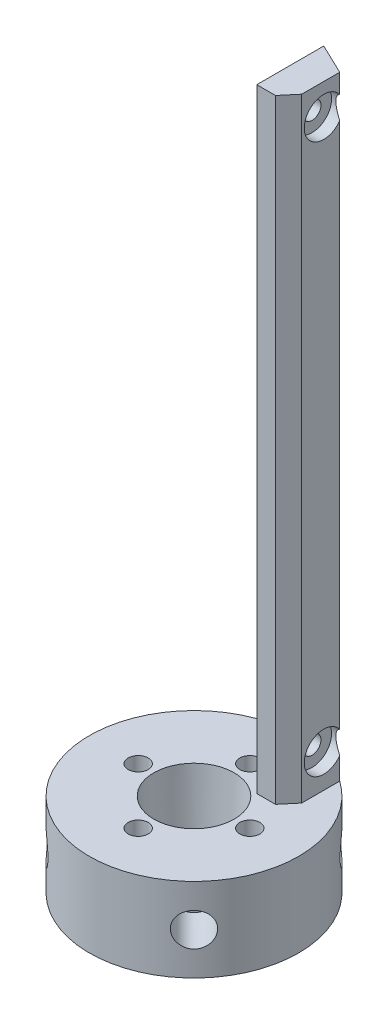
SolidWorks part; units mm, degrees
ref_plane "Ebene vorne" through (0, 0, 0) normal (0, 0, 1) x (1, 0, 0)
ref_plane "Ebene oben" through (0, 0, 0) normal (0, 1, 0) x (1, 0, 0)
ref_plane "Ebene rechts" through (0, 0, 0) normal (1, 0, 0) x (0, 0, -1)
sketch "Skizze1" plane through (0, 0, 0) normal (0, 1, 0) x (1, 0, 0)
  circle A0 centre (0, 0) radius 18.75
  dimension "D1" = 37.5
extrude "Aufsatz-Linear austragen1" add sketch "Skizze1" along normal blind 15
sketch "Skizze2" plane through (0, 15, 0) normal (0, 1, 0) x (1, 0, 0)
  circle A0 centre (0, 10) radius 1.8
  circle A1 centre (10, 0) radius 1.8
  circle A2 centre (0, -10) radius 1.8
  circle A3 centre (-10, 0) radius 1.8
  circle A4 centre (0, 0) radius 1.65
  point P12 (0, 0)
  dimension "D1" = 3.6
  dimension "D5" = 3.3
  dimension "D2" = 0
  dimension "D3" = 10
  dimension "D4" = 4
extrude "Schnitt-Linear austragen1" cut sketch "Skizze2" against normal through all
sketch "Skizze4" plane through (0, 15, 0) normal (0, 1, 0) x (1, 0, 0)
  line L0 (5.25, 17) -> (5.25, 6)
  line L4 (8.6073, 6) -> (10.7509, 8.5546)
  line L5 (5.25, 17) -> (5.25, 18)
  line L6 (10.7509, 8.5546) -> (10.7509, 15.3617)
  line L8 (5.25, 6) -> (8.6073, 6)
  arc A0 (10.7509, 15.3617) -> (5.25, 18) centre (0, 0) ccw
  dimension "D1" = 37.5
  dimension "D2" = 5.25
  dimension "D3" = 5.5009
  dimension "D4" = 17
  dimension "D5" = 40
  dimension "D6" = 5.5009
  dimension "D8" = 6.807
  dimension "D9" = 12
extrude "Aufsatz-Linear austragen2" add sketch "Skizze4" along normal blind 110
ref_plane "Ebene3" through (13.2583, 0, 13.2583) normal (0.7071, 0, 0.7071) x (0, -1, 0)
sketch "Skizze10" plane through (13.2583, 0, 13.2583) normal (0.7071, 0, 0.7071) x (0, -1, 0)
  line L0 (0, 20.625) -> (0, -20.625) construction
  circle A0 centre (-7.5, 0) radius 3
  dimension "D2" = 6
  dimension "D1" = 7.5
  dimension "D3" = 0
extrude "Schnitt-Linear austragen5" cut sketch "Skizze10" against normal blind 8
pattern_circular "Kreismuster1" count 4 every 90 about axis through (0, 0, 0) along (0, 1, 0) of "Schnitt-Linear austragen5"
sketch "Skizze11" plane through (5.25, 0, 0) normal (-1, 0, 0) x (0, 0, 1)
  line L8 (0, -8.25) -> (0, 8.25) construction
  line L9 (-15, 122) -> (18, 122)
  line L10 (-15, 122) -> (-15, 18.5)
  line L11 (-15, 18.5) -> (18, 18.5)
  line L12 (18, 122) -> (18, 18.5)
  line L13 (-18, 125) -> (-6, 125) construction
  circle A2 centre (-12.5, 119.5) radius 1.6
  circle A3 centre (-12.5, 21) radius 1.6
  dimension "D7" = 3.2
  dimension "D10" = 2.5
  dimension "D8" = 3.2
  dimension "D1" = 103.5
  dimension "D2" = 33
  dimension "D3" = 15
  dimension "D4" = 3
  dimension "D5" = 2.5
  dimension "D6" = 2.5
  dimension "D9" = 2.5
extrude "Schnitt-Linear austragen6" cut sketch "Skizze11" against normal through all contours A2 | A3
sketch "Skizze15" plane through (0, 0, 0) normal (0, -1, 0) x (1, 0, 0)
  circle A0 centre (0, 0) radius 3.2
  dimension "D1" = 6.4
sketch "Skizze16" plane through (10.7509, 0, 0) normal (1, 0, 0) x (0, 0, -1)
  circle A0 centre (12.5, 119.5) radius 3.5
  circle A1 centre (12.5, 21) radius 3.5
  dimension "D1" = 7
  dimension "D2" = 7
extrude "Schnitt-Linear austragen10" cut sketch "Skizze16" against normal blind 2.1
sketch "Skizze17" plane through (0, 125, 0) normal (0, 1, 0) x (1, 0, 0)
  line L0 (5.25, 18) -> (10.7509, 15.3617)
  arc A0 (10.7509, 15.3617) -> (5.25, 18) centre (0, 0) ccw construction
  arc A1 (5.25, 18) -> (10.7509, 15.3617) centre (0, 0) ccw construction
  arc A2 (10.7509, 15.3617) -> (5.25, 18) centre (0, 0) ccw
  dimension "D1" = 6.1009
extrude "Schnitt-Linear austragen11" cut sketch "Skizze17" against normal through all
sketch "Skizze18" plane through (0, 0, 0) normal (0, 0, 1) x (1, 0, 0)
  line L0 (0, 0) -> (6, 0)
  line L1 (20.625, 0) -> (-20.625, 0) construction
  line L2 (6, 0) -> (7.2, 15)
  line L3 (18.75, 15) -> (-18.75, 15) construction
  line L4 (7.2, 15) -> (0, 15)
  line L5 (0, 15) -> (0, 0)
  dimension "D1" = 6
  dimension "D2" = 7.2
revolve "Schnitt-Rotation1" cut sketch "Skizze18" angle 360 about L5
